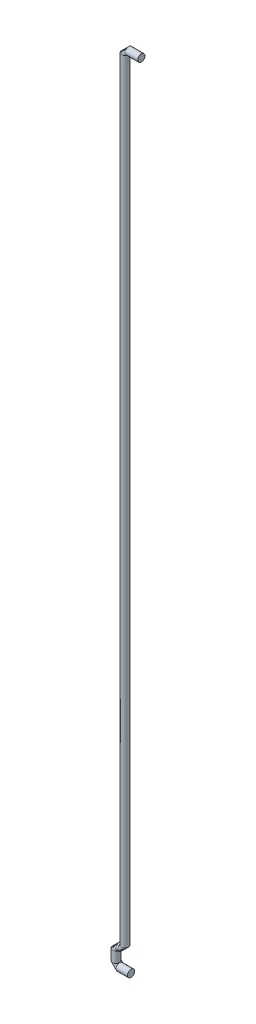
SolidWorks part; units mm, degrees
material "Copper"
ref_plane "Ebene vorne" through (0, 0, 0) normal (0, 0, 1) x (1, 0, 0)
ref_plane "Ebene oben" through (0, 0, 0) normal (0, 1, 0) x (1, 0, 0)
ref_plane "Ebene rechts" through (0, 0, 0) normal (1, 0, 0) x (0, 0, -1)
sketch "Sketch1" plane through (0, 0, 0) normal (0, 0, 1) x (1, 0, 0)
  line L0 (0, 6) -> (0, 220.1)
  line L1 (1, 221.1) -> (4.5, 221.1)
  line L3 (-1, 5) -> (-1.5, 5)
  line L4 (-2.5, 4) -> (-2.5, 1)
  line L6 (-1.5, 0) -> (1.65, 0)
  arc A0 (1, 221.1) -> (0, 220.1) centre (1, 220.1) ccw
  arc A1 (-1.5, 0) -> (-2.5, 1) centre (-1.5, 1) cw
  arc A2 (-1.5, 5) -> (-2.5, 4) centre (-1.5, 4) ccw
  arc A3 (0, 6) -> (-1, 5) centre (-1, 6) cw
  point P9 (0, 221.1)
  point P10 (0, 0)
  point P12 (0, 0)
  point P13 (-2.5, 0)
  point P14 (0, 0)
  point P19 (-2.5, 5)
  point P22 (0, 5)
  dimension "D4" = 1
  dimension "D5" = 1
  dimension "D1" = 4.5
  dimension "D2" = 221.1
  dimension "D3" = 1.65
  dimension "D6" = 2.5
  dimension "D7" = 5
ref_plane "Plane2" through (1.65, 0, 0) normal (1, 0, 0) x (0, 0, -1)
sketch "Sketch3" plane through (1.65, 0, 0) normal (1, 0, 0) x (0, 0, -1)
  circle A0 centre (0, 0) radius 1
  dimension "D1" = 2
sweep "Sweep3" add profiles "Sketch3" path "Sketch1"
